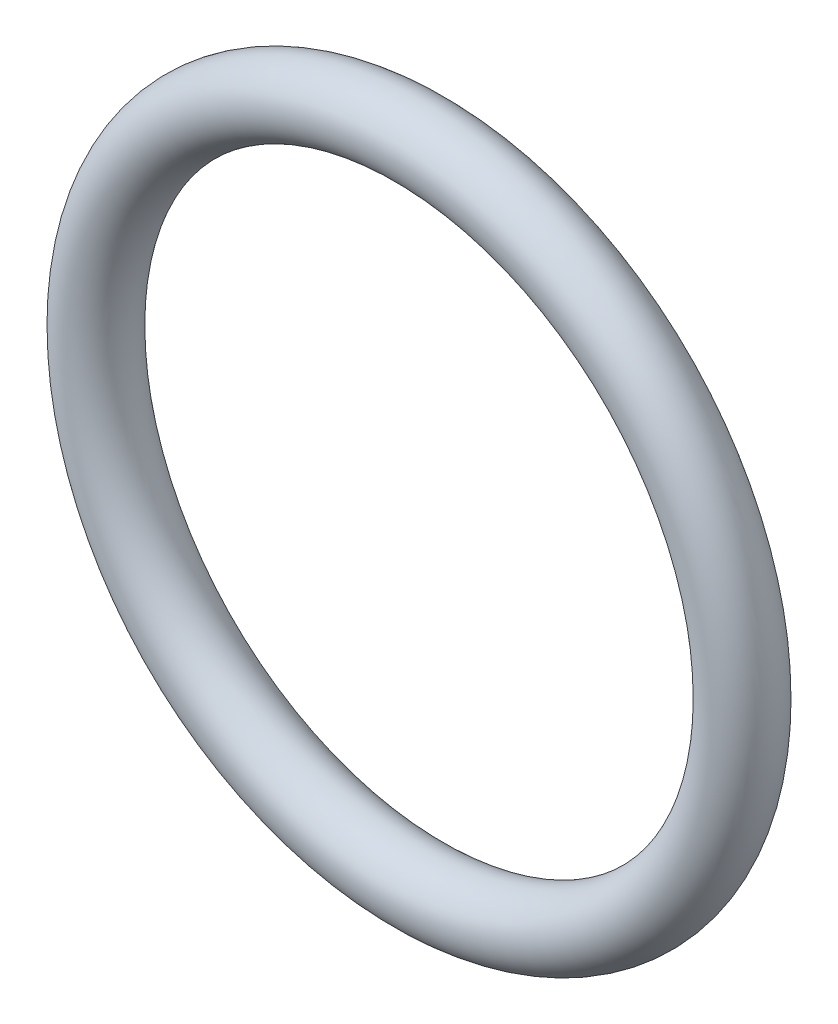
SolidWorks part; units mm, degrees
ref_plane "Front Plane" through (0, 0, 0) normal (0, 0, 1) x (1, 0, 0)
ref_plane "Top Plane" through (0, 0, 0) normal (0, 1, 0) x (1, 0, 0)
ref_plane "Right Plane" through (0, 0, 0) normal (1, 0, 0) x (0, 0, -1)
ref_plane "Plane1" through (0, 0, 0) normal (1, 0, 0) x (0, 0, -1)
sketch "Sketch1" plane through (0, 0, 0) normal (1, 0, 0) x (0, 0, -1)
  line L0 (0.7493, 0) -> (-0.7493, 0) construction
  circle A0 centre (0, 6.9977) radius 0.7493
revolve "Revolve1" add sketch "Sketch1" angle 360 about L0
